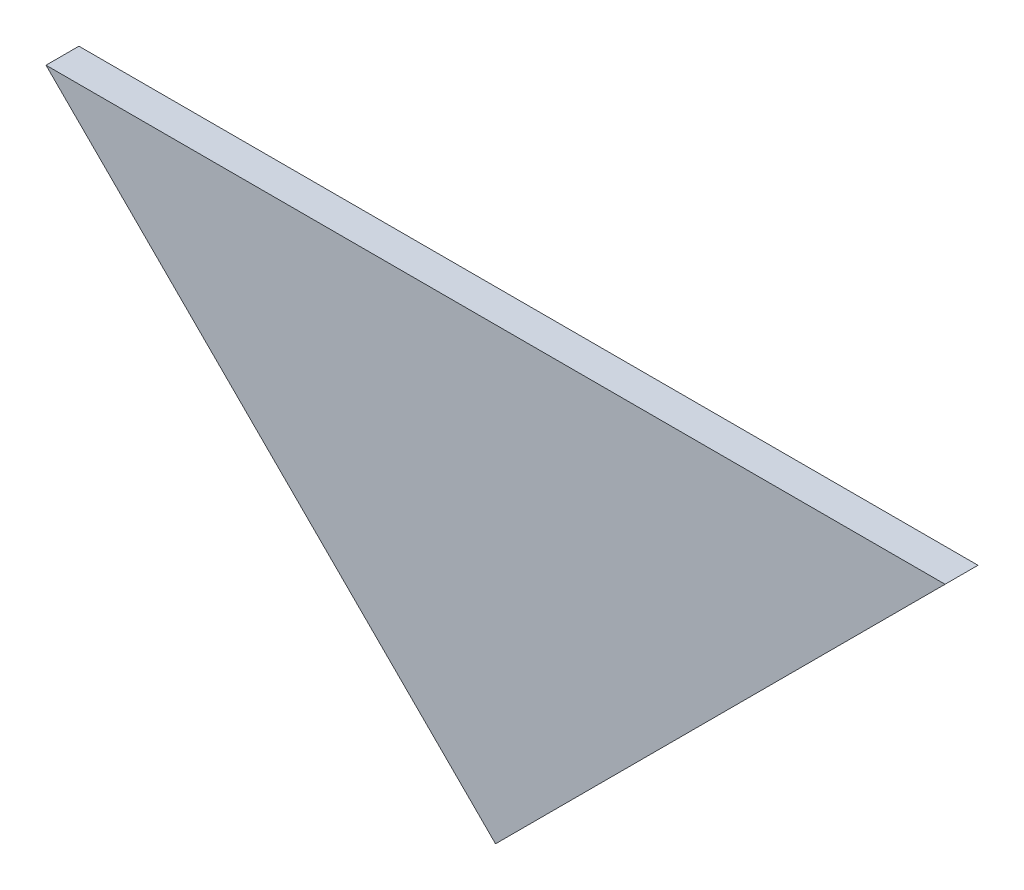
SolidWorks part; units mm, degrees
material "Acrylic (Medium-high impact)"
ref_plane "Front Plane" through (0, 0, 0) normal (0, 0, 1) x (1, 0, 0)
ref_plane "Top Plane" through (0, 0, 0) normal (0, 1, 0) x (1, 0, 0)
ref_plane "Right Plane" through (0, 0, 0) normal (1, 0, 0) x (0, 0, -1)
ref_plane "Plane1" through (0, 0, 113.7049) normal (0, 0, 1) x (1, 0, 0)
sketch "Sketch1" plane through (0, 0, 113.7049) normal (0, 0, 1) x (1, 0, 0)
  line L0 (40.966, -116.2449) -> (-40.966, -116.2449) construction
  line L1 (-40.966, -116.2449) -> (0, -157.2109) construction
  line L2 (0, -157.2109) -> (40.966, -116.2449) construction
  line L3 (40.966, -116.2449) -> (-40.966, -116.2449)
  line L4 (-40.966, -116.2449) -> (0, -157.2109)
  line L5 (0, -157.2109) -> (40.966, -116.2449)
extrude "Boss-Extrude1" add sketch "Sketch1" against normal mid plane 3
